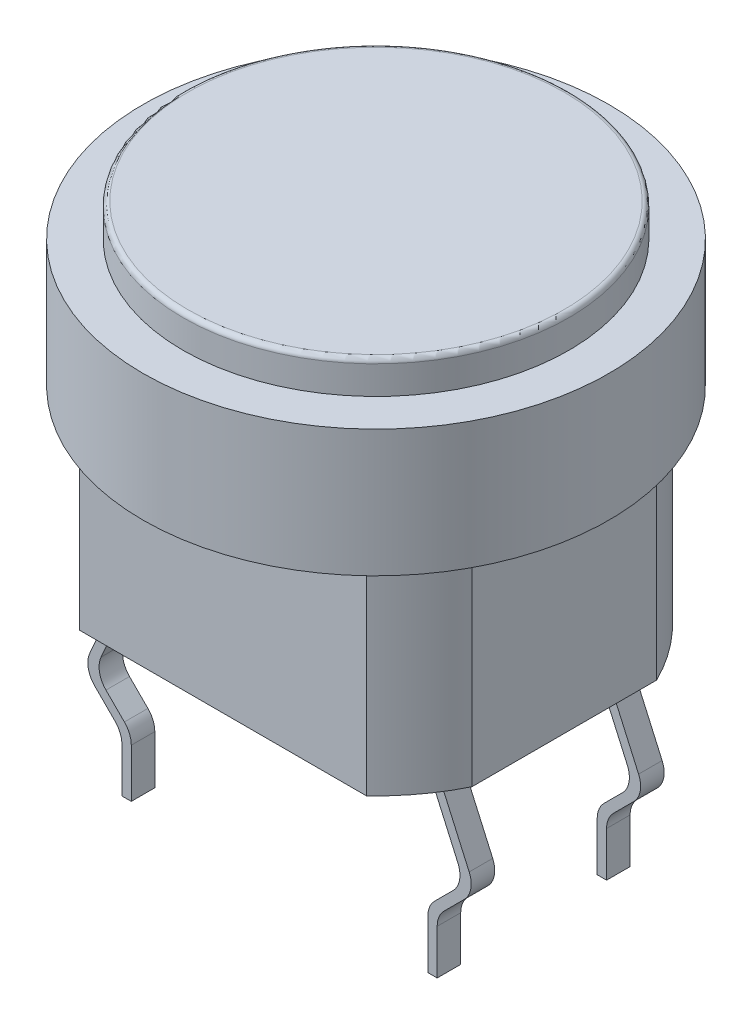
SolidWorks part; units mm, degrees
ref_plane "Front Plane" through (0, 0, 0) normal (0, 0, 1) x (1, 0, 0)
ref_plane "Top Plane" through (0, 0, 0) normal (0, 1, 0) x (1, 0, 0)
ref_plane "Right Plane" through (0, 0, 0) normal (1, 0, 0) x (0, 0, -1)
sketch "Sketch1" plane through (0, 0, 0) normal (0, 1, 0) x (1, 0, 0)
  circle A0 centre (0, 0) radius 4.95
  dimension "D1" = 9.9
extrude "Boss-Extrude1" add sketch "Sketch1" along normal blind 2.7
sketch "Sketch2" plane through (0, 2.7, 0) normal (0, 1, 0) x (1, 0, 0)
  circle A0 centre (0, 0) radius 4.1
  dimension "D1" = 8.2
extrude "Boss-Extrude2" add sketch "Sketch2" along normal blind 0.7
sketch "Sketch3" plane through (0, 0, 0) normal (0, -1, 0) x (1, 0, 0)
  line L1 (-4, 3.25) -> (4, 3.25)
  line L2 (-4, 3.25) -> (-4, -3.25)
  line L3 (-4, -3.25) -> (4, -3.25)
  line L4 (4, 3.25) -> (4, -3.25)
  line L5 (-4, 3.25) -> (4, -3.25) construction
  line L6 (-4, -3.25) -> (4, 3.25) construction
  circle A0 centre (0, 0) radius 4.455
  dimension "D3" = 8.91
  dimension "D1" = 6.5
  dimension "D2" = 8
extrude "Boss-Extrude3" add sketch "Sketch3" along normal blind 4.4 contours L3 A0 L4 L1 L2
sketch "Sketch4" plane through (0, 0, 3.25) normal (0, 0, 1) x (1, 0, 0)
  line L0 (-3.25, -4.4) -> (-4.05, -6.2)
  line L1 (-3.0471, -4.4) -> (3.0471, -4.4) construction
  line L2 (-4.05, -6.2) -> (-3.25, -7)
  line L3 (-3.25, -7) -> (-3.25, -8.2)
  line L4 (0, 0) -> (0, -8.2) construction
  line L5 (0, -8.2) -> (-3.25, -8.2) construction
  line L7 (3.25, -7) -> (3.25, -8.2)
  line L8 (4.05, -6.2) -> (3.25, -7)
  line L9 (3.25, -4.4) -> (4.05, -6.2)
  dimension "D1" = 3.25
  dimension "D2" = 3.8
  dimension "D3" = 0.8
  dimension "D4" = 1.8
  dimension "D5" = 0.8
  dimension "D6" = 0.8
extrude "Extrude-Thin1" add sketch "Sketch4" against normal blind 0.5 from offset 1.2 separate body thin thin type mid plane wall 0.2 offset against normal yes
fillet "Fillet1" radius 0.5 4 edges at (-3.15, -6.9586, 1.8) (-3.35, -7.0414, 1.8) (-4.1693, -6.2221, 1.8) (-3.9307, -6.1779, 1.8)
fillet "Fillet2" radius 0.5 4 edges at (3.15, -6.9586, 1.8) (3.35, -7.0414, 1.8) (4.1693, -6.2221, 1.8) (3.9307, -6.1779, 1.8)
sketch "Sketch5" plane through (2.1691, -4.8804, 0) normal (-0.4061, 0.9138, 0) x (0.9138, 0.4061, 0)
  line L4 (1.2829, -2.05) -> (1.2829, -1.55)
  line L5 (1.2829, -1.55) -> (1.0829, -1.55)
  line L6 (1.0829, -1.55) -> (1.0829, -2.05)
  line L7 (1.0829, -2.05) -> (1.2829, -2.05)
  line L8 (1.2829, -2.05) -> (1.2829, -1.55)
  line L9 (1.2829, -1.55) -> (1.0829, -1.55)
  line L10 (1.0829, -1.55) -> (1.0829, -2.05)
  line L11 (1.0829, -2.05) -> (1.2829, -2.05)
  dimension "D1" = 0
extrude "Boss-Extrude4" add sketch "Sketch5" along normal up to surface (0.0444 mm away)
sketch "Sketch6" plane through (-2.1691, -4.8804, 0) normal (0.4061, 0.9138, 0) x (0.9138, -0.4061, 0)
  line L4 (-1.2829, -1.55) -> (-1.2829, -2.05)
  line L5 (-1.2829, -2.05) -> (-1.0829, -2.05)
  line L6 (-1.0829, -2.05) -> (-1.0829, -1.55)
  line L7 (-1.0829, -1.55) -> (-1.2829, -1.55)
  line L8 (-1.2829, -1.55) -> (-1.2829, -2.05)
  line L9 (-1.2829, -2.05) -> (-1.0829, -2.05)
  line L10 (-1.0829, -2.05) -> (-1.0829, -1.55)
  line L11 (-1.0829, -1.55) -> (-1.2829, -1.55)
  dimension "D1" = 0
extrude "Boss-Extrude5" add sketch "Sketch6" along normal up to surface (0.0444 mm away)
mirror "Mirror2" about plane through (0, 0, 0) normal (0, 0, 1) of bodies 108 104
fillet "Fillet3" radius 0.1 1 edges at (0, 3.4, 4.1)
